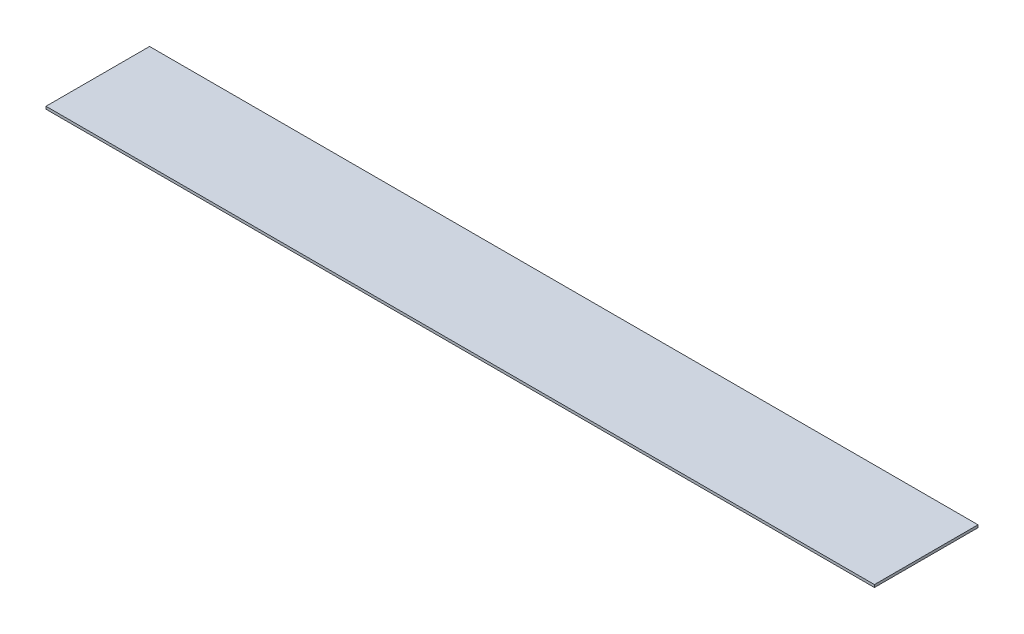
SolidWorks part; units mm, degrees
ref_plane "Front Plane" through (0, 0, 0) normal (0, 0, 1) x (1, 0, 0)
ref_plane "Top Plane" through (0, 0, 0) normal (0, 1, 0) x (1, 0, 0)
ref_plane "Right Plane" through (0, 0, 0) normal (1, 0, 0) x (0, 0, -1)
sketch "Sketch1" plane through (0, 0, 0) normal (0, 1, 0) x (1, 0, 0)
  line L1 (0, 0) -> (406.4, 0)
  line L2 (0, 0) -> (0, 50.8)
  line L3 (0, 50.8) -> (406.4, 50.8)
  line L4 (406.4, 0) -> (406.4, 50.8)
  dimension "D1" = 50.8
  dimension "D2" = 406.4
extrude "Boss-Extrude1" add sketch "Sketch1" along normal blind 1.27
